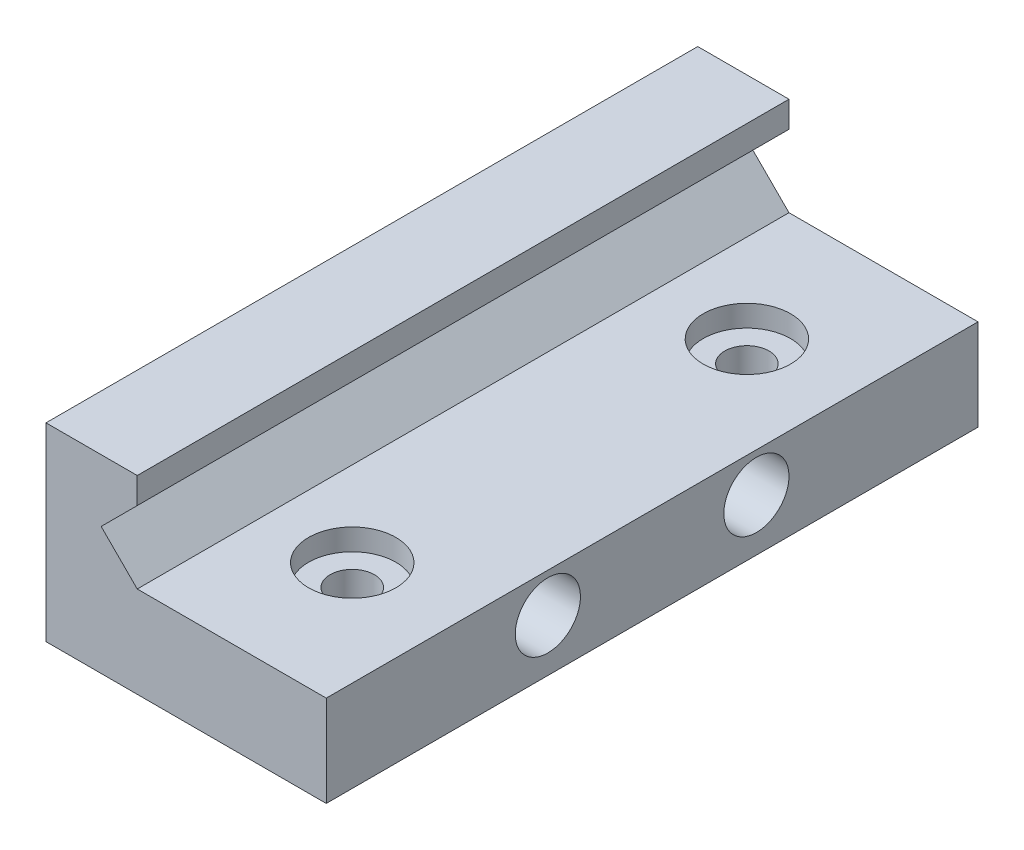
SolidWorks part; units mm, degrees
ref_plane "Front Plane" through (0, 0, 0) normal (0, 0, 1) x (1, 0, 0)
ref_plane "Top Plane" through (0, 0, 0) normal (0, 1, 0) x (1, 0, 0)
ref_plane "Right Plane" through (0, 0, 0) normal (1, 0, 0) x (0, 0, -1)
sketch "Sketch2" plane through (0, 0, 0) normal (0, 0, 1) x (1, 0, 0)
  line L0 (-52.0364, 78.4753) -> (-6.3368, 78.4753) construction
  line L1 (-15.7135, 63.6371) -> (-18.4835, 60.8671)
  line L2 (-18.4835, 60.8671) -> (-15.7135, 58.0971)
  line L3 (-15.7135, 58.0971) -> (-1.2135, 58.0971)
  line L4 (-15.7135, 59.2283) -> (-15.7135, 49.8296) construction
  line L5 (-22.7135, 51.0971) -> (-22.7135, 65.6371)
  line L6 (-22.7135, 65.6371) -> (-15.7135, 65.6371)
  line L7 (-15.7135, 65.6371) -> (-15.7135, 63.6371)
  line L8 (-1.2135, 58.0971) -> (-1.2135, 51.0971)
  line L9 (-1.2135, 51.0971) -> (-22.7135, 51.0971)
  dimension "D1" = 7
  dimension "D2" = 2
  dimension "D3" = 2.77
  dimension "D4" = 90
  dimension "D5" = 14.5
  dimension "D6" = 5.54
  dimension "D7" = 7
extrude "Boss-Extrude1" add sketch "Sketch2" along normal blind 50
sketch "Sketch3" plane through (-22.7135, 0, 0) normal (-1, 0, 0) x (0, 0, 1)
  line L0 (50, 51.0971) -> (0, 51.0971) construction
  line L3 (50, 65.6371) -> (50, 51.0971) construction
  line L4 (0, 65.6371) -> (0, 51.0971) construction
  circle A0 centre (17, 55.0971) radius 2.5
  circle A1 centre (33, 55.0971) radius 2.5
  dimension "D1" = 4
  dimension "D2" = 5
  dimension "D3" = 4
  dimension "D4" = 17
  dimension "D5" = 17
extrude "Cut-Extrude1" cut sketch "Sketch3" against normal up to next
hole_wizard "CBORE for M3 SBHCS1" positions "Sketch9" profile "Sketch8" counterbore size "M3" standard "ANSI Metric" end condition through all
sketch "Sketch9" plane through (0, 58.0971, 0) normal (0, 1, 0) x (1, 0, 0)
  line L1 (-1.2135, -50) -> (-1.2135, 0) construction
  line L2 (-1.2135, 0) -> (-15.7135, 0) construction
  line L3 (-1.2135, -50) -> (-15.7135, -50) construction
  point P0 (-9.2198, -40)
  point P2 (-8.9435, -10)
  dimension "D1" = 7.73
  dimension "D2" = 10
  dimension "D3" = 10
sketch "Sketch8" plane through (-9.2198, 58.0971, 40) normal (1, 0, 0) x (0, 0, 1)
  line L0 (0, 0) -> (0, 7)
  line L1 (0, 7) -> (1.7, 7)
  line L3 (1.7, 7) -> (1.7, 1.65)
  line L4 (1.7, 1.65) -> (3.35, 1.65)
  line L5 (3.35, 1.65) -> (3.35, 0)
  line L7 (3.35, 0) -> (0, 0)
  line L11 (0, -6.35) -> (0, 107.95) construction
  dimension "Thru Hole Dia." = 3.4
  dimension "Thru Hole Depth" = 7
  dimension "C'Bore Dia." = 6.7
  dimension "C'Bore Depth" = 1.65
